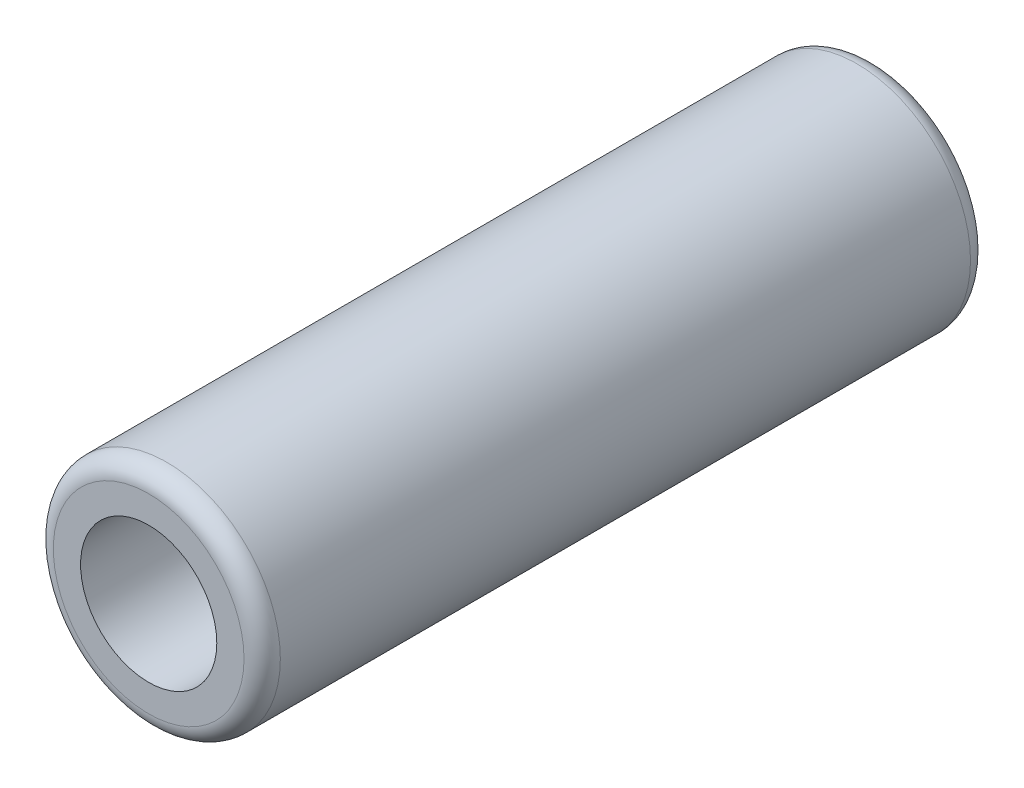
SolidWorks part; units mm, degrees
ref_plane "Front Plane" through (0, 0, 0) normal (0, 0, 1) x (1, 0, 0)
ref_plane "Top Plane" through (0, 0, 0) normal (0, 1, 0) x (1, 0, 0)
ref_plane "Right Plane" through (0, 0, 0) normal (1, 0, 0) x (0, 0, -1)
sketch "Sketch1" plane through (0, 0, 0) normal (0, 0, 1) x (1, 0, 0)
  circle A0 centre (0, 0) radius 37.5
  circle A1 centre (0, 0) radius 62.5
  dimension "D1" = 125
  dimension "D2" = 75
extrude "Boss-Extrude1" add sketch "Sketch1" along normal mid plane 400
fillet "Fillet1" radius 10 2 edges at (62.5, 0, -200) (62.5, 0, 200)
